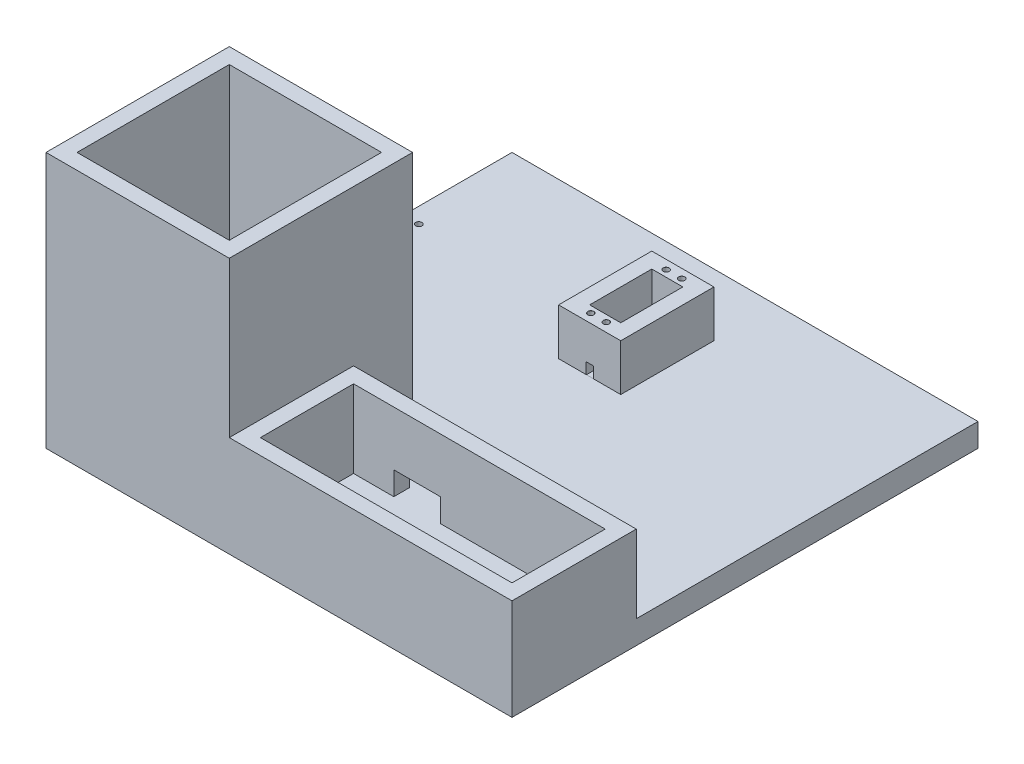
SolidWorks part; units mm, degrees
ref_plane "Alzado" through (0, 0, 0) normal (0, 0, 1) x (1, 0, 0)
ref_plane "Planta" through (0, 0, 0) normal (0, 1, 0) x (1, 0, 0)
ref_plane "Vista lateral" through (0, 0, 0) normal (1, 0, 0) x (0, 0, -1)
sketch "Croquis1" plane through (0, 0, 0) normal (0, 1, 0) x (1, 0, 0)
  line L1 (-150, -150) -> (150, -150)
  line L2 (-150, -150) -> (-150, 150)
  line L3 (-150, 150) -> (150, 150)
  line L4 (150, -150) -> (150, 150)
  line L5 (-150, -150) -> (150, 150) construction
  line L6 (-150, 150) -> (150, -150) construction
  point P0 (0, 0)
  dimension "D1" = 300
  dimension "D2" = 300
extrude "Saliente-Extruir1" add sketch "Croquis1" along normal blind 15
sketch "Croquis2" plane through (0, 15, 0) normal (0, 1, 0) x (1, 0, 0)
  line L1 (-150, -150) -> (-32, -150)
  line L2 (-150, -150) -> (-150, -55)
  line L3 (-140, -42) -> (-42, -42)
  line L4 (-32, -150) -> (-32, -55)
  line L5 (-140, -140) -> (-42, -140)
  line L6 (-150, -140) -> (-150, -32)
  line L7 (-150, -32) -> (-32, -32)
  line L8 (-42, -140) -> (-42, -42)
  line L9 (-32, -32) -> (-32, -55)
  line L10 (-140, -42) -> (-140, -140)
  line M12 (-150, 150) -> (-150, -150)
  line M13 (-150, -150) -> (150, -150)
  dimension "D1" = 10
  dimension "D2" = 118
  dimension "D3" = 118
  dimension "D4" = 108
  dimension "D5" = 98
extrude "Saliente-Extruir2" add sketch "Croquis2" along normal blind 150 contours L9 L7 L2 L4 L10 L3 L8 L5 M12 M13
sketch "Croquis3" plane through (0, 15, 0) normal (0, 1, 0) x (1, 0, 0)
  line L1 (0, 150) -> (0, -150) construction
  line L2 (150, 150) -> (-150, 150) construction
  line L3 (-32, -150) -> (150, -150) construction
  line L4 (-150, 0) -> (150, 0) construction
  line L5 (-150, 150) -> (-150, -32) construction
  line L6 (150, -150) -> (150, 150) construction
  line L8 (-10, 60) -> (10, 60)
  line L9 (-10, 60) -> (-10, 100)
  line L10 (-10, 100) -> (10, 100)
  line L11 (10, 60) -> (10, 100)
  line L12 (-10, 60) -> (10, 100) construction
  line L13 (-10, 100) -> (10, 60) construction
  line L14 (20, 50) -> (-20, 50)
  line L15 (20, 50) -> (20, 110)
  line L16 (20, 110) -> (-20, 110)
  line L17 (-20, 50) -> (-20, 110)
  line L18 (20, 50) -> (-20, 110) construction
  line L19 (20, 110) -> (-20, 50) construction
  circle A1 centre (0, 80) radius 75
  dimension "D1" = 150
  dimension "D2" = 70
  dimension "D3" = 40
  dimension "D4" = 20
  dimension "D5" = 40
  dimension "D6" = 60
extrude "Saliente-Extruir3" add sketch "Croquis3" along normal blind 30 contours L17 L14 L15 L16 L11 L8 L9 L10
sketch "Croquis4" plane through (0, 15, 0) normal (0, 1, 0) x (1, 0, 0)
  line L0 (-72.311, 50) -> (84.4779, 50) construction
  line L1 (0, 115.673) -> (0, -10.7976) construction
  line L2 (150, -150) -> (150, 150) construction
  line L3 (-32, -150) -> (150, -150)
  line L4 (-32, -150) -> (-32, -70)
  line L5 (-32, -70) -> (150, -70)
  line L6 (150, -150) -> (150, -70)
  line L8 (-22, -140) -> (140, -140)
  line L9 (-22, -140) -> (-22, -80)
  line L10 (-22, -80) -> (140, -80)
  line L11 (140, -140) -> (140, -80)
  dimension "D2" = 80
  dimension "D3" = 10
  dimension "D4" = 10
  dimension "D5" = 60
  dimension "D6" = 10
extrude "Saliente-Extruir4" add sketch "Croquis4" along normal blind 50
hole_wizard "Taladro de margen para M3.51" positions "Croquis5" profile "Croquis6" hole size "M3.5" standard "Ansi Metric"
sketch "Croquis5" plane through (0, 45, 0) normal (0, 1, 0) x (1, 0, 0)
  line L0 (20, 110) -> (-20, 110) construction
  line L1 (0, 83.4722) -> (0, 15.1443) construction
  line L2 (20, 50) -> (-20, 50) construction
  point P0 (-5, 104.25)
  point P2 (5, 104.25)
  point P4 (-5, 55.75)
  point P6 (5, 55.75)
  dimension "D1" = 5.75
  dimension "D2" = 48.5
  dimension "D3" = 10
  dimension "D4" = 10
  dimension "D5" = 48.5
  dimension "D6" = 5
  dimension "D7" = 5
  dimension "D8" = 5.75
sketch "Croquis6" plane through (-5, 45, -104.25) normal (1, 0, 0) x (0, 0, 1)
  line L0 (0, 0) -> (0, 16.1717)
  line L1 (0, 16.1717) -> (1.95, 15)
  line L2 (1.95, 15) -> (1.95, 0.025)
  line L3 (1.95, 0.025) -> (1.975, 0)
  line L5 (1.975, 0) -> (0, 0)
  line L6 (-1.95, 0.025) -> (-1.975, 0) construction
  line L10 (0, 16.1717) -> (-1.95, 15) construction
  line L11 (0, -6.35) -> (0, 107.95) construction
  dimension "Diámetro de taladro" = 3.9
  dimension "Profundidad de taladro" = 15
  dimension "Diámetro de avellanado cercano" = 3.95
  dimension "Ángulo de avellanado cercano" = 90
  dimension "Ángulo de perforador" = 118
sketch "Croquis7" plane through (0, 0, -50) normal (0, 0, 1) x (1, 0, 0)
  line L1 (-2.5, 14.5688) -> (2.5, 14.5688)
  line L2 (-2.5, 14.5688) -> (-2.5, 22.1774)
  line L3 (-2.5, 22.1774) -> (2.5, 22.1774)
  line L4 (2.5, 14.5688) -> (2.5, 22.1774)
  dimension "D1" = 17.5
extrude "Cortar-Extruir1" cut sketch "Croquis7" against normal up to vertex (10 mm away)
sketch "Croquis8" plane through (0, 0, 80) normal (0, 0, 1) x (1, 0, 0)
  line L0 (140, 15) -> (-22, 15) construction
  line L1 (3.9081, 15) -> (33.9081, 15)
  line L2 (3.9081, 15) -> (3.9081, 30)
  line L3 (3.9081, 30) -> (33.9081, 30)
  line L4 (33.9081, 15) -> (33.9081, 30)
  dimension "D1" = 15
  dimension "D2" = 30
extrude "Cortar-Extruir2" cut sketch "Croquis8" against normal blind 10
sketch "Croquis9" plane through (0, 15, 0) normal (0, 1, 0) x (1, 0, 0)
  line L0 (-10, 80) -> (-215.0189, 80) construction
  line L1 (-10, 60) -> (-10, 100) construction
  line L2 (-150, 150) -> (-150, -32) construction
  circle A0 centre (-140, 80) radius 2
  dimension "D1" = 4
  dimension "D2" = 10
extrude "Cortar-Extruir3" cut sketch "Croquis9" against normal blind 20
